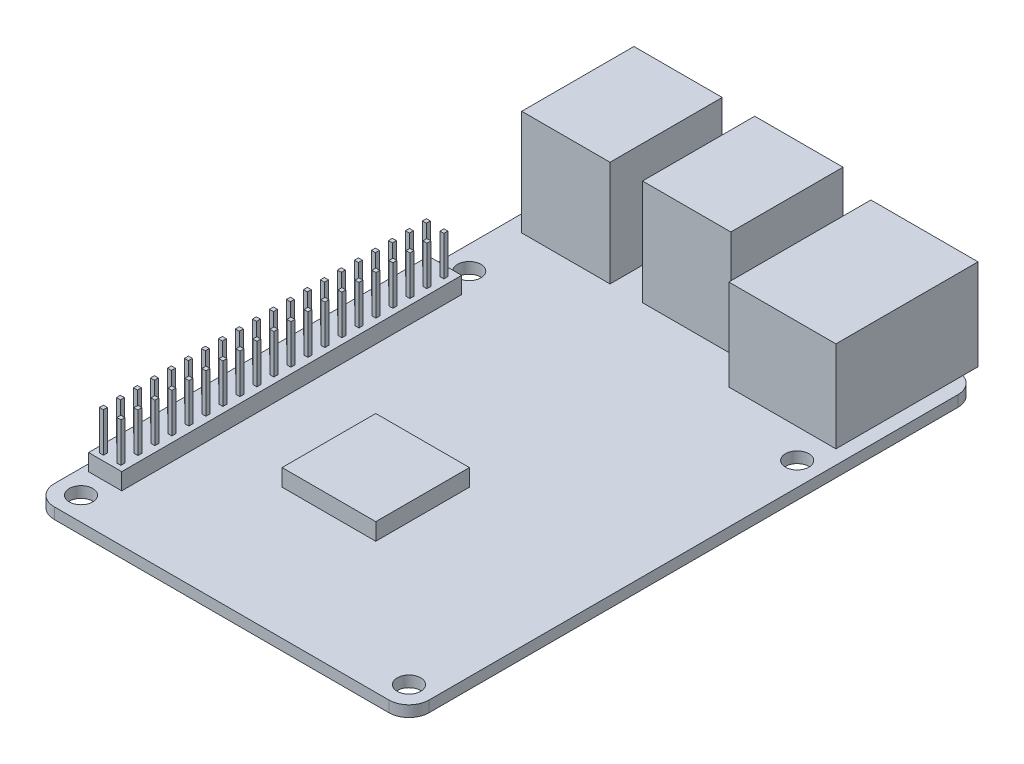
SolidWorks part; units mm, degrees
ref_plane "Front Plane" through (0, 0, 0) normal (0, 0, 1) x (1, 0, 0)
ref_plane "Top Plane" through (0, 0, 0) normal (0, 1, 0) x (1, 0, 0)
ref_plane "Right Plane" through (0, 0, 0) normal (1, 0, 0) x (0, 0, -1)
sketch "Sketch1" plane through (0, 0, 0) normal (0, 1, 0) x (1, 0, 0)
  line L5 (0, -10) -> (0, 0) construction
  line L7 (-24.5, -39) -> (24.5, -39) construction
  line L8 (-24.5, -39) -> (-24.5, 19) construction
  line L13 (-24.5, 19) -> (24.5, 19) construction
  line L14 (24.5, -39) -> (24.5, 19) construction
  line L15 (-24.5, -39) -> (24.5, 19) construction
  line L22 (-24.5, 19) -> (24.5, -39) construction
  line L23 (-25, -42.5) -> (25, -42.5)
  line L24 (-28, -39.5) -> (-28, 39.5)
  line L25 (-25, 42.5) -> (25, 42.5)
  line L26 (28, -39.5) -> (28, 39.5)
  line L27 (-28, -42.5) -> (28, 42.5) construction
  line L28 (-28, 42.5) -> (28, -42.5) construction
  line L29 (28, 0) -> (-28, 0) construction
  circle A22 centre (24.5, 19) radius 1.75
  circle A23 centre (-24.5, 19) radius 1.75
  circle A24 centre (-24.5, -39) radius 1.75
  circle A25 centre (24.5, -39) radius 1.75
  arc A26 (25, -42.5) -> (28, -39.5) centre (25, -39.5) ccw
  arc A27 (-25, -42.5) -> (-28, -39.5) centre (-25, -39.5) cw
  arc A28 (-28, 39.5) -> (-25, 42.5) centre (-25, 39.5) cw
  arc A29 (25, 42.5) -> (28, 39.5) centre (25, 39.5) cw
  point P2 (0, -10)
  point P14 (0, 0)
  dimension "D1" = 3.5
  dimension "D5" = 3
  dimension "D6" = 85
  dimension "D8" = 23.5
  dimension "D3" = 58
  dimension "D4" = 49
  dimension "D7" = 56
extrude "Boss-Extrude1" add sketch "Sketch1" along normal blind 1.651
sketch "Sketch2" plane through (0, 1.651, 0) normal (0, 1, 0) x (1, 0, 0)
  line L0 (-25.5108, 36.2389) -> (5.7312, 36.2389) construction
  line L1 (-25.5108, 44.6209) -> (-12.3155, 44.6209)
  line L2 (-25.5108, 44.6209) -> (-25.5108, 27.8569)
  line L3 (-25.5108, 27.8569) -> (-12.3155, 27.8569)
  line L4 (-12.3155, 44.6209) -> (-12.3155, 27.8569)
  line L5 (-7.4641, 44.6209) -> (5.7312, 44.6209)
  line L6 (-7.4641, 44.6209) -> (-7.4641, 27.8569)
  line L7 (-7.4641, 27.8569) -> (5.7312, 27.8569)
  line L8 (5.7312, 44.6209) -> (5.7312, 27.8569)
  line L9 (-28, 39.5) -> (-28, -39.5) construction
  line L11 (25, 42.5) -> (-25, 42.5) construction
  dimension "D1" = 13.1953
  dimension "D2" = 16.764
  dimension "D3" = 4.8514
  dimension "D4" = 2.4892
  dimension "D5" = 2.1209
extrude "Boss-Extrude2" add sketch "Sketch2" along normal blind 15.748
sketch "Sketch4" plane through (0, 1.651, 0) normal (0, 1, 0) x (1, 0, 0)
  line L0 (5.7312, 44.6209) -> (-7.4641, 44.6209) construction
  line L1 (9.8968, 44.6209) -> (25.8988, 44.6209)
  line L2 (9.8968, 44.6209) -> (9.8968, 23.389)
  line L3 (9.8968, 23.389) -> (25.8988, 23.389)
  line L4 (25.8988, 44.6209) -> (25.8988, 23.389)
  line L5 (5.7312, 27.8569) -> (5.7312, 44.6209) construction
  dimension "D1" = 16.002
  dimension "D2" = 21.2319
  dimension "D3" = 4.1656
extrude "Boss-Extrude3" add sketch "Sketch4" along normal blind 13.589
sketch "Sketch3" plane through (0, 0, -44.6209) normal (0, 0, -1) x (-1, 0, 0)
  line L0 (12.3155, 1.651) -> (25.5108, 1.651) construction
  line L1 (25.5108, 1.651) -> (25.5108, 17.399) construction
  line L2 (25.5108, 17.399) -> (12.3155, 17.399) construction
  line L3 (12.3155, 17.399) -> (12.3155, 1.651) construction
  line L4 (-5.7312, 1.651) -> (7.4641, 1.651) construction
  line L5 (7.4641, 1.651) -> (7.4641, 17.399) construction
  line L6 (7.4641, 17.399) -> (-5.7312, 17.399) construction
  line L7 (-5.7312, 17.399) -> (-5.7312, 1.651) construction
  line L8 (12.3155, 1.651) -> (25.5108, 1.651) construction
  line L9 (25.5108, 1.651) -> (25.5108, 17.399) construction
  line L10 (25.5108, 17.399) -> (12.3155, 17.399) construction
  line L11 (12.3155, 17.399) -> (12.3155, 1.651) construction
  line L12 (-5.7312, 1.651) -> (7.4641, 1.651) construction
  line L13 (7.4641, 1.651) -> (7.4641, 17.399) construction
  line L14 (7.4641, 17.399) -> (-5.7312, 17.399) construction
  line L15 (-5.7312, 17.399) -> (-5.7312, 1.651) construction
  line L16 (13.5855, 2.921) -> (24.2408, 2.921)
  line L17 (24.2408, 2.921) -> (24.2408, 8.89)
  line L18 (24.2408, 16.129) -> (13.5855, 16.129)
  line L19 (13.5855, 16.129) -> (13.5855, 10.16)
  line L20 (-4.4612, 2.921) -> (6.1941, 2.921)
  line L21 (6.1941, 2.921) -> (6.1941, 8.89)
  line L22 (6.1941, 16.129) -> (-4.4612, 16.129)
  line L23 (-4.4612, 16.129) -> (-4.4612, 10.16)
  line L24 (-24.6288, 2.921) -> (-11.1668, 2.921)
  line L25 (-11.1668, 2.921) -> (-11.1668, 13.97)
  line L26 (-11.1668, 13.97) -> (-24.6288, 13.97)
  line L27 (-24.6288, 13.97) -> (-24.6288, 2.921)
  line L28 (-25.8988, 1.651) -> (-9.8968, 1.651)
  line L29 (-9.8968, 1.651) -> (-9.8968, 15.24)
  line L30 (-9.8968, 15.24) -> (-25.8988, 15.24)
  line L31 (-25.8988, 15.24) -> (-25.8988, 1.651)
  line L32 (-25.8988, 1.651) -> (-9.8968, 1.651) construction
  line L33 (-9.8968, 1.651) -> (-9.8968, 15.24) construction
  line L34 (-9.8968, 15.24) -> (-25.8988, 15.24) construction
  line L35 (-25.8988, 15.24) -> (-25.8988, 1.651) construction
  line L36 (-4.4612, 9.525) -> (6.1941, 9.525) construction
  line L37 (13.5855, 9.525) -> (24.2408, 9.525) construction
  line L38 (-4.4612, 8.89) -> (6.1941, 8.89)
  line L39 (13.5855, 8.89) -> (24.2408, 8.89)
  line L40 (-4.4612, 10.16) -> (6.1941, 10.16)
  line L41 (13.5855, 10.16) -> (24.2408, 10.16)
  line L42 (13.5855, 8.89) -> (13.5855, 2.921)
  line L43 (13.5855, 16.129) -> (13.5855, 2.921) construction
  line L44 (24.2408, 10.16) -> (24.2408, 16.129)
  line L45 (24.2408, 2.921) -> (24.2408, 16.129) construction
  line L46 (6.1941, 10.16) -> (6.1941, 16.129)
  line L47 (6.1941, 2.921) -> (6.1941, 16.129) construction
  line L48 (-4.4612, 8.89) -> (-4.4612, 2.921)
  line L49 (-4.4612, 16.129) -> (-4.4612, 2.921) construction
  dimension "D1" = 1.27
  dimension "D2" = 0
  dimension "D3" = 1.27
  dimension "D4" = 0.635
  dimension "D5" = 0.635
extrude "Cut-Extrude1" cut sketch "Sketch3" against normal blind 15.748
sketch "Sketch5" plane through (0, 1.651, 0) normal (0, 1, 0) x (1, 0, 0)
  line L0 (-24.5, 19) -> (-24.5, 15.4) construction
  line L1 (-26.9765, 15.4) -> (-22.0235, 15.4)
  line L2 (-26.9765, 15.4) -> (-26.9765, -35.4)
  line L3 (-26.9765, -35.4) -> (-22.0235, -35.4)
  line L4 (-22.0235, 15.4) -> (-22.0235, -35.4)
  line L5 (-24.5, -39) -> (-24.5, -35.4) construction
  dimension "D1" = 50.8
  dimension "D2" = 4.953
extrude "Boss-Extrude4" add sketch "Sketch5" along normal blind 2.4892
sketch "Sketch6" plane through (0, 4.1402, 0) normal (0, 1, 0) x (1, 0, 0)
  line L0 (-25.8081, 13.9077) -> (-23.1919, 13.9077) construction
  line L3 (-24.5, 15.4) -> (-24.5, -35.4) construction
  line L4 (-26.1065, 13.6093) -> (-25.5096, 13.6093)
  line L5 (-26.1065, 13.6093) -> (-26.1065, 14.2062)
  line L6 (-26.1065, 14.2062) -> (-25.5096, 14.2062)
  line L7 (-25.5096, 13.6093) -> (-25.5096, 14.2062)
  line L8 (-26.1065, 13.6093) -> (-25.5096, 14.2062) construction
  line L9 (-26.1065, 14.2062) -> (-25.5096, 13.6093) construction
  line L10 (-23.4903, 13.6093) -> (-22.8934, 13.6093)
  line L11 (-23.4903, 13.6093) -> (-23.4903, 14.2062)
  line L12 (-23.4903, 14.2062) -> (-22.8934, 14.2062)
  line L13 (-22.8934, 13.6093) -> (-22.8934, 14.2062)
  line L14 (-23.4903, 13.6093) -> (-22.8934, 14.2062) construction
  line L15 (-23.4903, 14.2062) -> (-22.8934, 13.6093) construction
  line L16 (-22.0235, 15.4) -> (-26.9765, 15.4) construction
  line L17 (-26.9765, -35.4) -> (-22.0235, -35.4) construction
  line L18 (-26.1065, 11.0693) -> (-25.5096, 11.0693)
  line L19 (-26.1065, 11.0693) -> (-26.1065, 11.6662)
  line L20 (-25.5096, 11.0693) -> (-25.5096, 11.6662)
  line L21 (-26.1065, 11.6662) -> (-25.5096, 11.6662)
  line L22 (-25.8081, 11.3677) -> (-23.1919, 11.3677) construction
  line L23 (-23.4903, 11.0693) -> (-23.4903, 11.6662)
  line L24 (-23.4903, 11.6662) -> (-22.8934, 11.6662)
  line L25 (-22.8934, 11.0693) -> (-22.8934, 11.6662)
  line L26 (-23.4903, 11.0693) -> (-22.8934, 11.0693)
  line L27 (-26.1065, 8.5293) -> (-25.5096, 8.5293)
  line L28 (-26.1065, 8.5293) -> (-26.1065, 9.1262)
  line L29 (-25.5096, 8.5293) -> (-25.5096, 9.1262)
  line L30 (-26.1065, 9.1262) -> (-25.5096, 9.1262)
  line L31 (-25.8081, 8.8277) -> (-23.1919, 8.8277) construction
  line L32 (-23.4903, 8.5293) -> (-23.4903, 9.1262)
  line L33 (-23.4903, 9.1262) -> (-22.8934, 9.1262)
  line L34 (-22.8934, 8.5293) -> (-22.8934, 9.1262)
  line L35 (-23.4903, 8.5293) -> (-22.8934, 8.5293)
  line L36 (-26.1065, 5.9893) -> (-25.5096, 5.9893)
  line L37 (-26.1065, 5.9893) -> (-26.1065, 6.5862)
  line L38 (-25.5096, 5.9893) -> (-25.5096, 6.5862)
  line L39 (-26.1065, 6.5862) -> (-25.5096, 6.5862)
  line L40 (-25.8081, 6.2877) -> (-23.1919, 6.2877) construction
  line L41 (-23.4903, 5.9893) -> (-23.4903, 6.5862)
  line L42 (-23.4903, 6.5862) -> (-22.8934, 6.5862)
  line L43 (-22.8934, 5.9893) -> (-22.8934, 6.5862)
  line L44 (-23.4903, 5.9893) -> (-22.8934, 5.9893)
  line L45 (-26.1065, 3.4493) -> (-25.5096, 3.4493)
  line L46 (-26.1065, 3.4493) -> (-26.1065, 4.0462)
  line L47 (-25.5096, 3.4493) -> (-25.5096, 4.0462)
  line L48 (-26.1065, 4.0462) -> (-25.5096, 4.0462)
  line L49 (-25.8081, 3.7477) -> (-23.1919, 3.7477) construction
  line L50 (-23.4903, 3.4493) -> (-23.4903, 4.0462)
  line L51 (-23.4903, 4.0462) -> (-22.8934, 4.0462)
  line L52 (-22.8934, 3.4493) -> (-22.8934, 4.0462)
  line L53 (-23.4903, 3.4493) -> (-22.8934, 3.4493)
  line L54 (-26.1065, 0.9093) -> (-25.5096, 0.9093)
  line L55 (-26.1065, 0.9093) -> (-26.1065, 1.5062)
  line L56 (-25.5096, 0.9093) -> (-25.5096, 1.5062)
  line L57 (-26.1065, 1.5062) -> (-25.5096, 1.5062)
  line L58 (-25.8081, 1.2077) -> (-23.1919, 1.2077) construction
  line L59 (-23.4903, 0.9093) -> (-23.4903, 1.5062)
  line L60 (-23.4903, 1.5062) -> (-22.8934, 1.5062)
  line L61 (-22.8934, 0.9093) -> (-22.8934, 1.5062)
  line L62 (-23.4903, 0.9093) -> (-22.8934, 0.9093)
  line L63 (-26.1065, -1.6307) -> (-25.5096, -1.6307)
  line L64 (-26.1065, -1.6307) -> (-26.1065, -1.0338)
  line L65 (-25.5096, -1.6307) -> (-25.5096, -1.0338)
  line L66 (-26.1065, -1.0338) -> (-25.5096, -1.0338)
  line L67 (-25.8081, -1.3323) -> (-23.1919, -1.3323) construction
  line L68 (-23.4903, -1.6307) -> (-23.4903, -1.0338)
  line L69 (-23.4903, -1.0338) -> (-22.8934, -1.0338)
  line L70 (-22.8934, -1.6307) -> (-22.8934, -1.0338)
  line L71 (-23.4903, -1.6307) -> (-22.8934, -1.6307)
  line L72 (-26.1065, -4.1707) -> (-25.5096, -4.1707)
  line L73 (-26.1065, -4.1707) -> (-26.1065, -3.5738)
  line L74 (-25.5096, -4.1707) -> (-25.5096, -3.5738)
  line L75 (-26.1065, -3.5738) -> (-25.5096, -3.5738)
  line L76 (-25.8081, -3.8723) -> (-23.1919, -3.8723) construction
  line L77 (-23.4903, -4.1707) -> (-23.4903, -3.5738)
  line L78 (-23.4903, -3.5738) -> (-22.8934, -3.5738)
  line L79 (-22.8934, -4.1707) -> (-22.8934, -3.5738)
  line L80 (-23.4903, -4.1707) -> (-22.8934, -4.1707)
  line L81 (-26.1065, -6.7107) -> (-25.5096, -6.7107)
  line L82 (-26.1065, -6.7107) -> (-26.1065, -6.1138)
  line L83 (-25.5096, -6.7107) -> (-25.5096, -6.1138)
  line L84 (-26.1065, -6.1138) -> (-25.5096, -6.1138)
  line L85 (-25.8081, -6.4123) -> (-23.1919, -6.4123) construction
  line L86 (-23.4903, -6.7107) -> (-23.4903, -6.1138)
  line L87 (-23.4903, -6.1138) -> (-22.8934, -6.1138)
  line L88 (-22.8934, -6.7107) -> (-22.8934, -6.1138)
  line L89 (-23.4903, -6.7107) -> (-22.8934, -6.7107)
  line L90 (-26.1065, -9.2507) -> (-25.5096, -9.2507)
  line L91 (-26.1065, -9.2507) -> (-26.1065, -8.6538)
  line L92 (-25.5096, -9.2507) -> (-25.5096, -8.6538)
  line L93 (-26.1065, -8.6538) -> (-25.5096, -8.6538)
  line L94 (-25.8081, -8.9523) -> (-23.1919, -8.9523) construction
  line L95 (-23.4903, -9.2507) -> (-23.4903, -8.6538)
  line L96 (-23.4903, -8.6538) -> (-22.8934, -8.6538)
  line L97 (-22.8934, -9.2507) -> (-22.8934, -8.6538)
  line L98 (-23.4903, -9.2507) -> (-22.8934, -9.2507)
  line L99 (-26.1065, -11.7907) -> (-25.5096, -11.7907)
  line L100 (-26.1065, -11.7907) -> (-26.1065, -11.1938)
  line L101 (-25.5096, -11.7907) -> (-25.5096, -11.1938)
  line L102 (-26.1065, -11.1938) -> (-25.5096, -11.1938)
  line L103 (-25.8081, -11.4923) -> (-23.1919, -11.4923) construction
  line L104 (-23.4903, -11.7907) -> (-23.4903, -11.1938)
  line L105 (-23.4903, -11.1938) -> (-22.8934, -11.1938)
  line L106 (-22.8934, -11.7907) -> (-22.8934, -11.1938)
  line L107 (-23.4903, -11.7907) -> (-22.8934, -11.7907)
  line L108 (-26.1065, -14.3307) -> (-25.5096, -14.3307)
  line L109 (-26.1065, -14.3307) -> (-26.1065, -13.7338)
  line L110 (-25.5096, -14.3307) -> (-25.5096, -13.7338)
  line L111 (-26.1065, -13.7338) -> (-25.5096, -13.7338)
  line L112 (-25.8081, -14.0323) -> (-23.1919, -14.0323) construction
  line L113 (-23.4903, -14.3307) -> (-23.4903, -13.7338)
  line L114 (-23.4903, -13.7338) -> (-22.8934, -13.7338)
  line L115 (-22.8934, -14.3307) -> (-22.8934, -13.7338)
  line L116 (-23.4903, -14.3307) -> (-22.8934, -14.3307)
  line L117 (-26.1065, -16.8707) -> (-25.5096, -16.8707)
  line L118 (-26.1065, -16.8707) -> (-26.1065, -16.2738)
  line L119 (-25.5096, -16.8707) -> (-25.5096, -16.2738)
  line L120 (-26.1065, -16.2738) -> (-25.5096, -16.2738)
  line L121 (-25.8081, -16.5723) -> (-23.1919, -16.5723) construction
  line L122 (-23.4903, -16.8707) -> (-23.4903, -16.2738)
  line L123 (-23.4903, -16.2738) -> (-22.8934, -16.2738)
  line L124 (-22.8934, -16.8707) -> (-22.8934, -16.2738)
  line L125 (-23.4903, -16.8707) -> (-22.8934, -16.8707)
  line L126 (-26.1065, -19.4107) -> (-25.5096, -19.4107)
  line L127 (-26.1065, -19.4107) -> (-26.1065, -18.8138)
  line L128 (-25.5096, -19.4107) -> (-25.5096, -18.8138)
  line L129 (-26.1065, -18.8138) -> (-25.5096, -18.8138)
  line L130 (-25.8081, -19.1123) -> (-23.1919, -19.1123) construction
  line L131 (-23.4903, -19.4107) -> (-23.4903, -18.8138)
  line L132 (-23.4903, -18.8138) -> (-22.8934, -18.8138)
  line L133 (-22.8934, -19.4107) -> (-22.8934, -18.8138)
  line L134 (-23.4903, -19.4107) -> (-22.8934, -19.4107)
  line L135 (-26.1065, -21.9507) -> (-25.5096, -21.9507)
  line L136 (-26.1065, -21.9507) -> (-26.1065, -21.3538)
  line L137 (-25.5096, -21.9507) -> (-25.5096, -21.3538)
  line L138 (-26.1065, -21.3538) -> (-25.5096, -21.3538)
  line L139 (-25.8081, -21.6523) -> (-23.1919, -21.6523) construction
  line L140 (-23.4903, -21.9507) -> (-23.4903, -21.3538)
  line L141 (-23.4903, -21.3538) -> (-22.8934, -21.3538)
  line L142 (-22.8934, -21.9507) -> (-22.8934, -21.3538)
  line L143 (-23.4903, -21.9507) -> (-22.8934, -21.9507)
  line L144 (-26.1065, -24.4907) -> (-25.5096, -24.4907)
  line L145 (-26.1065, -24.4907) -> (-26.1065, -23.8938)
  line L146 (-25.5096, -24.4907) -> (-25.5096, -23.8938)
  line L147 (-26.1065, -23.8938) -> (-25.5096, -23.8938)
  line L148 (-25.8081, -24.1923) -> (-23.1919, -24.1923) construction
  line L149 (-23.4903, -24.4907) -> (-23.4903, -23.8938)
  line L150 (-23.4903, -23.8938) -> (-22.8934, -23.8938)
  line L151 (-22.8934, -24.4907) -> (-22.8934, -23.8938)
  line L152 (-23.4903, -24.4907) -> (-22.8934, -24.4907)
  line L153 (-26.1065, -27.0307) -> (-25.5096, -27.0307)
  line L154 (-26.1065, -27.0307) -> (-26.1065, -26.4338)
  line L155 (-25.5096, -27.0307) -> (-25.5096, -26.4338)
  line L156 (-26.1065, -26.4338) -> (-25.5096, -26.4338)
  line L157 (-25.8081, -26.7323) -> (-23.1919, -26.7323) construction
  line L158 (-23.4903, -27.0307) -> (-23.4903, -26.4338)
  line L159 (-23.4903, -26.4338) -> (-22.8934, -26.4338)
  line L160 (-22.8934, -27.0307) -> (-22.8934, -26.4338)
  line L161 (-23.4903, -27.0307) -> (-22.8934, -27.0307)
  line L162 (-26.1065, -29.5707) -> (-25.5096, -29.5707)
  line L163 (-26.1065, -29.5707) -> (-26.1065, -28.9738)
  line L164 (-25.5096, -29.5707) -> (-25.5096, -28.9738)
  line L165 (-26.1065, -28.9738) -> (-25.5096, -28.9738)
  line L166 (-25.8081, -29.2723) -> (-23.1919, -29.2723) construction
  line L167 (-23.4903, -29.5707) -> (-23.4903, -28.9738)
  line L168 (-23.4903, -28.9738) -> (-22.8934, -28.9738)
  line L169 (-22.8934, -29.5707) -> (-22.8934, -28.9738)
  line L170 (-23.4903, -29.5707) -> (-22.8934, -29.5707)
  line L171 (-26.1065, -32.1107) -> (-25.5096, -32.1107)
  line L172 (-26.1065, -32.1107) -> (-26.1065, -31.5138)
  line L173 (-25.5096, -32.1107) -> (-25.5096, -31.5138)
  line L174 (-26.1065, -31.5138) -> (-25.5096, -31.5138)
  line L175 (-25.8081, -31.8123) -> (-23.1919, -31.8123) construction
  line L176 (-23.4903, -32.1107) -> (-23.4903, -31.5138)
  line L177 (-23.4903, -31.5138) -> (-22.8934, -31.5138)
  line L178 (-22.8934, -32.1107) -> (-22.8934, -31.5138)
  line L179 (-23.4903, -32.1107) -> (-22.8934, -32.1107)
  line L180 (-26.1065, -34.6507) -> (-25.5096, -34.6507)
  line L181 (-26.1065, -34.6507) -> (-26.1065, -34.0538)
  line L182 (-25.5096, -34.6507) -> (-25.5096, -34.0538)
  line L183 (-26.1065, -34.0538) -> (-25.5096, -34.0538)
  line L184 (-25.8081, -34.3523) -> (-23.1919, -34.3523) construction
  line L185 (-23.4903, -34.6507) -> (-23.4903, -34.0538)
  line L186 (-23.4903, -34.0538) -> (-22.8934, -34.0538)
  line L187 (-22.8934, -34.6507) -> (-22.8934, -34.0538)
  line L188 (-23.4903, -34.6507) -> (-22.8934, -34.6507)
  point P6 (-25.8081, 13.9077)
  point P11 (-23.1919, 13.9077)
  point P18 (-24.5, 13.9077)
  dimension "D1" = 0.5969
  dimension "D2" = 2.0193
  dimension "D3" = 1.1938
  dimension "D4" = 20
extrude "Boss-Extrude5" add sketch "Sketch6" along normal blind 5.8928
sketch "Sketch7" plane through (0, 1.651, 0) normal (0, 1, 0) x (1, 0, 0)
  line L0 (-22.0235, -35.4) -> (-22.0235, 15.4) construction
  line L1 (-10.5173, -8.9466) -> (3.4781, -8.9466)
  line L2 (-10.5173, -8.9466) -> (-10.5173, -22.942)
  line L3 (-10.5173, -22.942) -> (3.4781, -22.942)
  line L4 (3.4781, -8.9466) -> (3.4781, -22.942)
  line L5 (-25, -42.5) -> (25, -42.5) construction
  dimension "D1" = 13.9954
  dimension "D2" = 11.5062
  dimension "D3" = 19.558
extrude "Boss-Extrude6" add sketch "Sketch7" along normal blind 2.54
